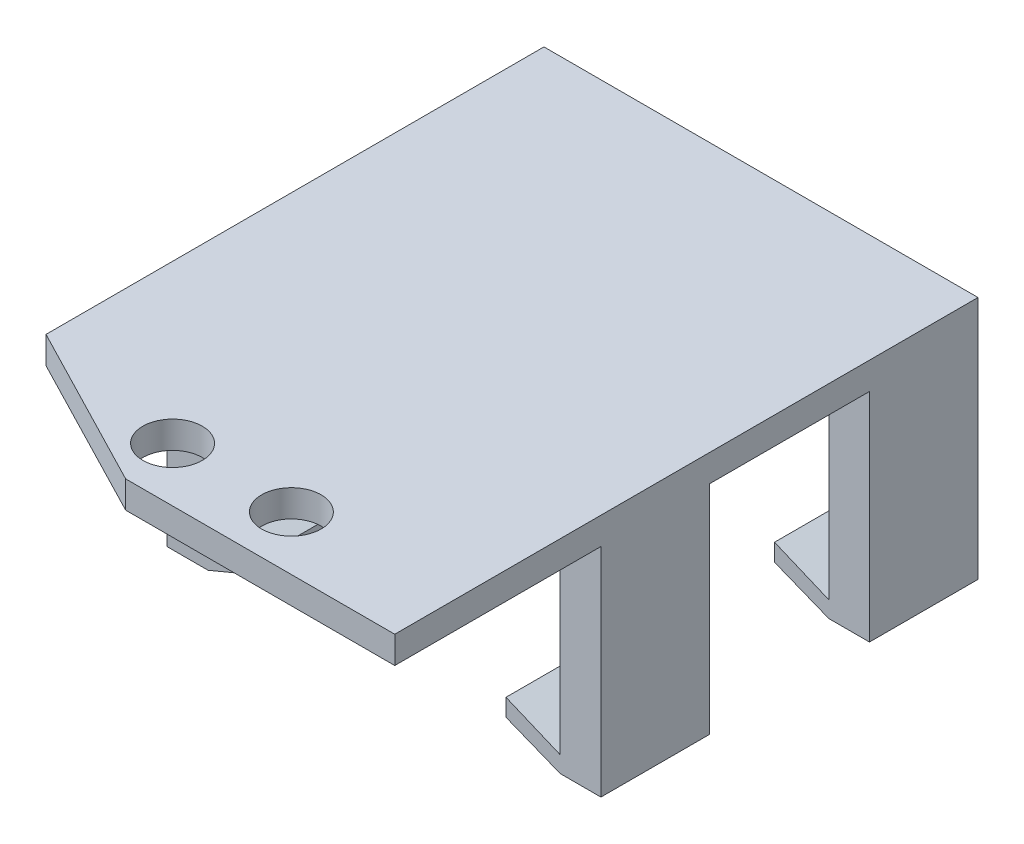
SolidWorks part; units mm, degrees
material "Custom Plastic"
ref_plane "Front Plane" through (0, 0, 0) normal (0, 0, 1) x (1, 0, 0)
ref_plane "Top Plane" through (0, 0, 0) normal (0, 1, 0) x (1, 0, 0)
ref_plane "Right Plane" through (0, 0, 0) normal (1, 0, 0) x (0, 0, -1)
sketch "Sketch3" plane through (0, 0, 0) normal (0, 1, 0) x (1, 0, 0)
  line L0 (29.1227, -39.629) -> (18.8853, -29.3915) construction
  line L1 (-11.5173, 12.441) -> (29.1227, 12.441)
  line L2 (-11.5173, 12.441) -> (-11.5173, -42.169)
  line L3 (-11.5173, -42.169) -> (18.8853, -42.169)
  line L4 (29.1227, 12.441) -> (29.1227, -34.5642)
  line L6 (21.4177, -26.8591) -> (29.1227, -34.5642) construction
  line L12 (18.8853, -42.169) -> (29.1227, -42.169)
  line L13 (29.1227, -42.169) -> (29.1227, -34.5642)
  circle A0 centre (3.2401, -37.089) radius 2.7813
  circle A2 centre (14.3653, -37.089) radius 2.7813
  dimension "D2" = 5.5626
  dimension "D3" = 5.5626
  dimension "D1" = 5.08
  dimension "1" = 40.64
  dimension "D4" = 11.1252
  dimension "D7" = 5.08
  dimension "D9" = 135
  dimension "D10" = 14.478
  dimension "D11" = 3.5814
extrude "Boss-Extrude3" add sketch "Sketch3" along normal blind 2.54
sketch "Sketch4" plane through (0, 0, 0) normal (0, -1, 0) x (1, 0, 0)
  line L0 (-11.5173, -12.441) -> (-11.5173, 42.169) construction
  line L1 (-11.5173, 27.945) -> (-7.7073, 27.945)
  line L2 (-11.5173, 27.945) -> (-11.5173, -12.441)
  line L3 (-11.5173, -12.441) -> (-7.7073, -12.441)
  line L4 (-7.7073, 27.945) -> (-7.7073, -12.441)
  line L5 (29.1227, -12.441) -> (-11.5173, -12.441) construction
  line L6 (-11.5173, 42.169) -> (29.1227, 42.169) construction
  line L7 (29.1227, 42.169) -> (29.1227, -12.441) construction
  line L8 (29.1227, 27.945) -> (25.3127, 27.945)
  line L9 (29.1227, 27.945) -> (29.1227, -12.441)
  line L10 (29.1227, -12.441) -> (25.3127, -12.441)
  line L11 (25.3127, 27.945) -> (25.3127, -12.441)
  dimension "D1" = 14.224
  dimension "D2" = 3.81
  dimension "D3" = 14.224
  dimension "D4" = 3.81
extrude "Boss-Extrude4" add sketch "Sketch4" along normal blind 20.32
sketch "Sketch5" plane through (-7.7073, 0, 0) normal (1, 0, 0) x (0, 0, -1)
  line L0 (-27.945, -20.32) -> (-27.945, 0) construction
  line L1 (-27.945, -18.796) -> (12.441, -18.796)
  line L2 (-27.945, -18.796) -> (-27.945, -20.32)
  line L3 (-27.945, -20.32) -> (12.441, -20.32)
  line L4 (12.441, -18.796) -> (12.441, -20.32)
  dimension "D1" = 1.524
extrude "Boss-Extrude5" add sketch "Sketch5" along normal blind 5.08
sketch "Sketch6" plane through (25.3127, 0, 0) normal (-1, 0, 0) x (0, 0, 1)
  line L0 (-12.441, 2.54) -> (-12.441, -20.32) construction
  line L1 (-12.441, -18.796) -> (27.945, -18.796)
  line L2 (-12.441, -18.796) -> (-12.441, -20.32)
  line L3 (-12.441, -20.32) -> (27.945, -20.32)
  line L4 (27.945, -18.796) -> (27.945, -20.32)
  dimension "D1" = 1.524
extrude "Boss-Extrude6" add sketch "Sketch6" along normal blind 5.08
sketch "Sketch7" plane through (0, 0, 27.945) normal (0, 0, 1) x (1, 0, 0)
  line L1 (-11.5173, 0) -> (29.1227, 0)
  line L2 (-11.5173, 0) -> (-11.5173, -20.32)
  line L3 (-11.5173, -20.32) -> (29.1227, -20.32)
  line L4 (29.1227, 0) -> (29.1227, -20.32)
extrude "Cut-Extrude1" cut sketch "Sketch7" against normal blind 5.08
sketch "Sketch11" plane through (0, 0, 0) normal (0, -1, 0) x (1, 0, 0)
  line L1 (-11.5173, 22.865) -> (29.1227, 22.865)
  line L2 (-11.5173, 22.865) -> (-11.5173, -12.441)
  line L3 (-11.5173, -12.441) -> (29.1227, -12.441)
  line L4 (29.1227, 22.865) -> (29.1227, -12.441)
extrude "Boss-Extrude7" add sketch "Sketch11" along normal blind 2.9718
sketch "Sketch12" plane through (0, 0, 22.865) normal (0, 0, 1) x (1, 0, 0)
  line L0 (-7.7073, -18.796) -> (-2.5934, -16.6688)
  line L1 (-2.5934, -16.6688) -> (-2.6273, -18.796)
  line L2 (-2.6273, -18.796) -> (-7.7073, -18.796)
  line L3 (20.2327, -18.796) -> (20.2327, -16.6688)
  line L4 (20.2327, -16.6688) -> (25.3127, -18.796)
  line L5 (25.3127, -18.796) -> (20.2327, -18.796)
  dimension "D1" = 2.1272
  dimension "D2" = 2.1272
extrude "Boss-Extrude8" add sketch "Sketch12" against normal up to surface (35.306 mm away) up to face at (8.8027, -13.1106, -12.441)
sketch "Sketch8" plane through (29.1227, 0, 0) normal (1, 0, 0) x (0, 0, -1)
  line L0 (12.441, -20.32) -> (-22.865, -20.32) construction
  line L1 (2.281, -20.32) -> (-12.705, -20.32)
  line L2 (2.281, -20.32) -> (2.281, 0)
  line L3 (2.281, 0) -> (-12.705, 0)
  line L4 (-12.705, -20.32) -> (-12.705, 0)
  line L5 (-42.169, 0) -> (-22.865, 0) construction
  line L6 (-22.865, -20.32) -> (-22.865, 0) construction
  line L7 (12.441, 2.54) -> (12.441, -20.32) construction
  dimension "D1" = 0
  dimension "D2" = 10.16
  dimension "D3" = 10.16
extrude "Cut-Extrude2" cut sketch "Sketch8" against normal through all
sketch "Sketch13" plane through (0, 0, 22.865) normal (0, 0, 1) x (1, 0, 0)
  line L0 (-7.6607, -20.32) -> (-2.618, -18.2165)
  line L1 (-11.5173, -20.32) -> (-2.6273, -20.32) construction
  line L2 (-2.6273, -18.796) -> (-2.5934, -16.6688) construction
  line L3 (-2.618, -18.2165) -> (-2.6273, -20.32)
  line L4 (-2.6273, -20.32) -> (-7.6607, -20.32)
  line L5 (20.2327, -20.32) -> (20.2048, -20.32)
  line L6 (20.2327, -20.32) -> (29.1227, -20.32) construction
  line L7 (20.2048, -20.32) -> (20.2327, -18.2946)
  line L8 (20.2327, -20.32) -> (20.2327, -16.6688) construction
  line L9 (20.2327, -18.2946) -> (20.2327, -20.32)
  line L10 (20.2327, -18.2946) -> (25.3127, -20.32)
  line L11 (25.3127, -20.32) -> (20.2327, -20.32)
  line M5 (20.2327, -16.6688) -> (20.2327, -20.32)
  line M6 (20.2327, -20.32) -> (29.1227, -20.32)
  line M10 (-11.5173, -20.32) -> (-2.6273, -20.32)
  line M11 (-2.6273, -20.32) -> (-2.6273, -18.796)
  line M12 (-2.6273, -18.796) -> (-2.5934, -16.6688)
  dimension "D1" = 2.1035
  dimension "D2" = 2.0254
extrude "Cut-Extrude3" cut sketch "Sketch13" against normal through all contours L0 M10 M11 M12 | L10 M5 M6
sketch "Sketch14" plane through (0, 0, 0) normal (0, -1, 0) x (1, 0, 0)
  circle A0 centre (3.2401, 37.089) radius 2.7813
  circle A1 centre (14.3653, 37.089) radius 2.7813
  circle A2 centre (3.2401, 37.089) radius 3.81
  circle A3 centre (14.3653, 37.089) radius 3.81
  dimension "D1" = 5.5626
  dimension "D2" = 5.5626
  dimension "D3" = 7.62
  dimension "D4" = 7.62
extrude "Boss-Extrude9" add sketch "Sketch14" against normal blind 2.54
sketch "Sketch15" plane through (0, 2.54, 0) normal (0, 1, 0) x (1, 0, 0)
  line L0 (18.8853, -42.169) -> (13.6783, -42.169) construction
  line L1 (-11.5173, -42.169) -> (29.1227, -42.169) construction
  line L2 (13.6783, -42.169) -> (29.1227, -42.169)
  line L4 (13.6783, -42.169) -> (18.8853, -39.4766)
  line L7 (13.6783, -42.169) -> (29.1227, -34.1831)
  line L8 (29.1227, -42.169) -> (29.1227, 12.441) construction
  line L9 (29.1227, -42.169) -> (29.1227, -34.1831)
  line L10 (8.8027, 12.441) -> (8.8027, -50.2652) construction
  line L11 (29.1227, 12.441) -> (-11.5173, 12.441) construction
  line L12 (3.9272, -42.169) -> (-11.5173, -34.1831)
  line L13 (-11.5173, -42.169) -> (-11.5173, -34.1831)
  line L14 (3.9272, -42.169) -> (-11.5173, -42.169)
  line M5 (-11.5173, 12.441) -> (-11.5173, -42.169)
  line M6 (-11.5173, -42.169) -> (29.1227, -42.169)
extrude "Cut-Extrude4" cut sketch "Sketch15" against normal through all contours L12 M6 M5
equation "\"D3@Sketch8\"=\"D2@Sketch8\""
